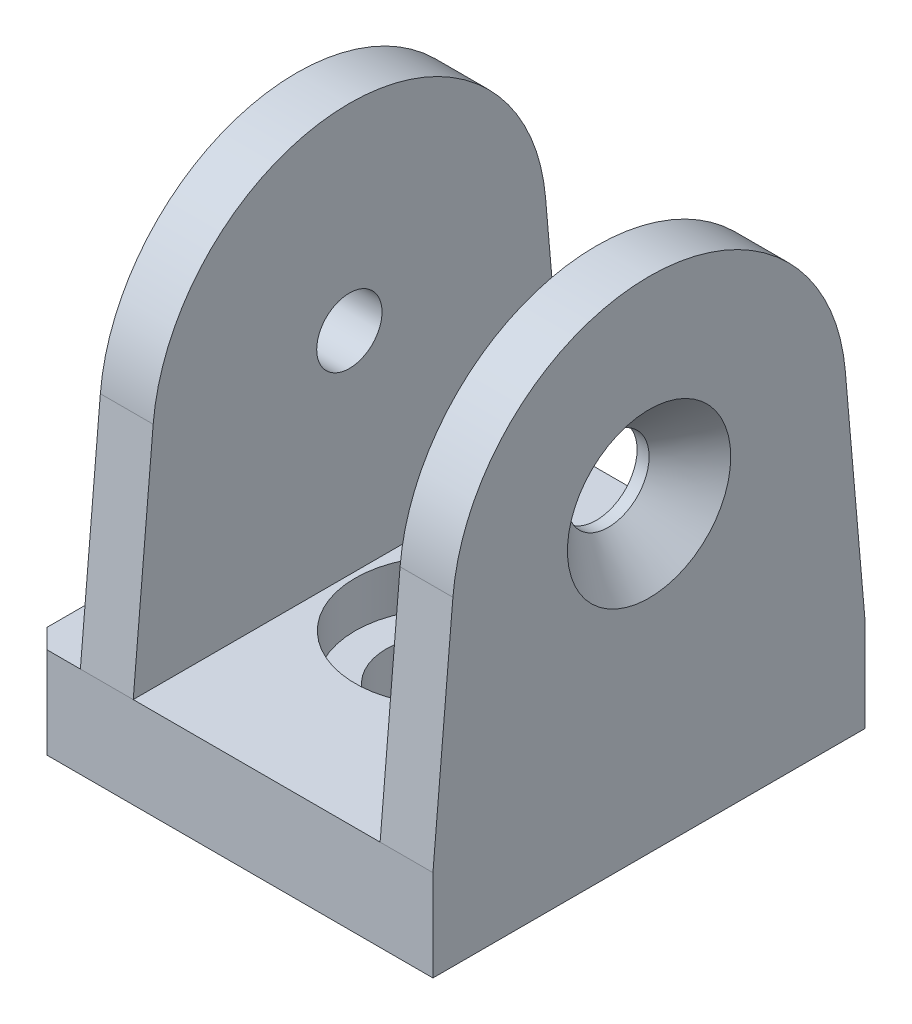
SolidWorks part; units mm, degrees
material "Алюминиевый сплав"
ref_plane "Спереди" through (0, 0, 0) normal (0, 0, 1) x (1, 0, 0)
ref_plane "Сверху" through (0, 0, 0) normal (0, 1, 0) x (1, 0, 0)
ref_plane "Справа" through (0, 0, 0) normal (1, 0, 0) x (0, 0, -1)
sketch "Эскиз1" plane through (0, 0, 0) normal (0, 1, 0) x (1, 0, 0)
  line L1 (21.1, -22.5) -> (-21.1, -22.5)
  line L2 (21.1, -22.5) -> (21.1, 22.5)
  line L3 (21.1, 22.5) -> (-21.1, 22.5)
  line L4 (-21.1, -22.5) -> (-21.1, 22.5)
  line L5 (21.1, -22.5) -> (-21.1, 22.5) construction
  line L6 (21.1, 22.5) -> (-21.1, -22.5) construction
  point P0 (0, 0)
  dimension "D1" = 42.2
  dimension "D2" = 45
extrude "Бобышка-Вытянуть1" add sketch "Эскиз1" along normal blind 9.5
sketch "Эскиз2" plane through (0, 0, 0) normal (0, 0, 1) x (1, 0, 0)
  line L1 (-21.1, 0) -> (21.1, 0) construction
  line L2 (-6.25, 0) -> (-6.25, 4.75)
  line L3 (-6.25, 4.75) -> (-9.5, 4.75)
  line L4 (-9.5, 4.75) -> (-9.5, 9.5)
  line L5 (-21.1, 9.5) -> (21.1, 9.5) construction
  line L7 (0, 9.5) -> (0, 0) construction
  line L11 (-21.1, 9.5) -> (-21.1, 0) construction
  line L12 (-9.5, 9.5) -> (0, 9.5)
  line L13 (0, 0) -> (-6.25, 0)
  line L14 (0, 0) -> (0, 9.5)
  point P17 (-21.1, 4.75)
  dimension "D1" = 12.5
  dimension "D2" = 19
revolve "Вырез-Повернуть1" cut sketch "Эскиз2" angle 360 about L7
sketch "Эскиз3" plane through (21.1, 0, 0) normal (1, 0, 0) x (0, 0, -1)
  line L0 (-22.5, 9.5) -> (-20.4222, 33.2841)
  line L1 (20.4222, 33.2841) -> (22.5, 9.5)
  line L2 (22.5, 9.5) -> (-22.5, 9.5)
  line L3 (-22.5, 0) -> (22.5, 0) construction
  arc A0 (-20.4222, 33.2841) -> (20.4222, 33.2841) centre (0, 31.5) cw
  dimension "D1" = 52
  dimension "D2" = 22
extrude "Бобышка-Вытянуть2" add sketch "Эскиз3" against normal blind 36.7
sketch "Эскиз4" plane through (0, 0, 0) normal (0, 0, 1) x (1, 0, 0)
  line L0 (-15.6, 9.5) -> (21.1, 9.5) construction
  line L1 (15.6, 9.5) -> (-10.1, 9.5)
  line L2 (15.6, 9.5) -> (15.6, 52)
  line L3 (15.6, 52) -> (-10.1, 52)
  line L4 (-10.1, 9.5) -> (-10.1, 52)
  line L5 (21.1, 52) -> (-15.6, 52) construction
  line L6 (15.6, 30.75) -> (21.1, 30.75) construction
  line L7 (21.1, 33.2841) -> (21.1, 9.5) construction
  line L8 (-10.1, 30.75) -> (-15.6, 30.75) construction
  line L9 (-15.6, 33.2841) -> (-15.6, 9.5) construction
  dimension "D1" = 5.5
extrude "Вырез-Вытянуть1" cut sketch "Эскиз4" against normal through all and the other way through all
chamfer "Фаска1" distance 2 angle 45 2 edges at (-21.1, 4.75, -22.5) (-21.1, 4.75, 22.5)
hole_wizard "Зенковка для винта с полупотайной головкой 1" positions "Эскиз8" profile "Эскиз10" countersink size "M8" standard "ISO" end condition up to next
sketch "Эскиз8" plane through (21.1, 0, 0) normal (1, 0, 0) x (0, 0, -1)
  point P0 (0, 31.5)
sketch "Эскиз10" plane through (21.1, 31.5, 0) normal (0, 1, 0) x (0, 0, -1)
  line L0 (0, 0) -> (0, 5.5)
  line L1 (0, 5.5) -> (4.25, 5.5)
  line L2 (4.25, 5.5) -> (4.25, 4.25)
  line L3 (4.25, 4.25) -> (8.5, 0)
  line L5 (8.5, 0) -> (0, 0)
  line L6 (-4.25, 4.25) -> (-8.5, 0) construction
  line L11 (0, -6.35) -> (0, 107.95) construction
  dimension "Диаметр сквозного отверстия" = 8.5
  dimension "Глубина сквозного отверстия" = 5.5
  dimension "Диаметр передней зенковки" = 17
  dimension "Угол передней зенковки" = 90
hole_wizard "Отверстие обработанное метчиком M81" positions "Эскиз11" profile "Эскиз13" tap size "M8" standard "ISO" end condition up to next
sketch "Эскиз11" plane through (-15.6, 0, 0) normal (-1, 0, 0) x (0, 0, 1)
  point P0 (0, 31.5)
sketch "Эскиз13" plane through (-15.6, 31.5, 0) normal (0, 1, 0) x (0, 0, 1)
  line L0 (0, 0) -> (0, 5.5)
  line L1 (0, 5.5) -> (3.4, 5.5)
  line L2 (3.4, 5.5) -> (3.4, 0)
  line L5 (3.4, 0) -> (0, 0)
  line L11 (0, -6.35) -> (0, 107.95) construction
  dimension "Диаметр проходного сверла" = 6.8
  dimension "Глубина проходного сверла" = 5.5
cosmetic thread "Отверстие резьбы2" parameters "D2"=8
